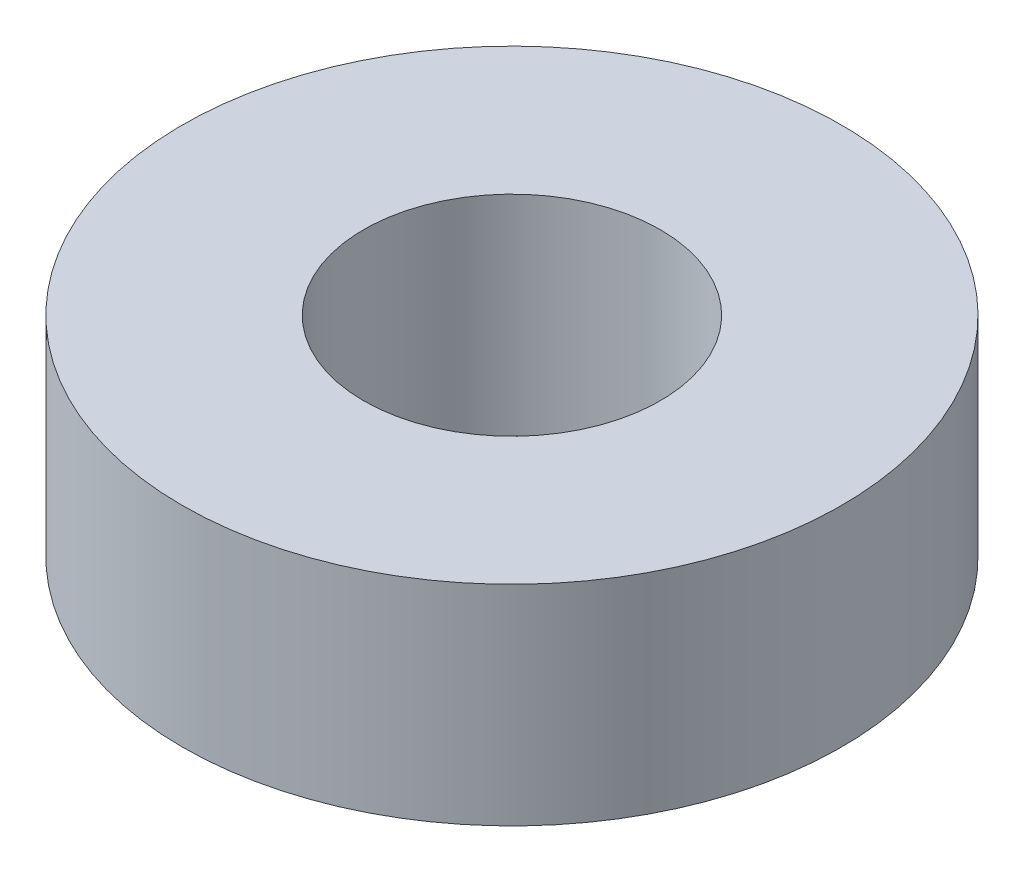
SolidWorks part; units mm, degrees
ref_plane "Front Plane" through (0, 0, 0) normal (0, 0, 1) x (1, 0, 0)
ref_plane "Top Plane" through (0, 0, 0) normal (0, 1, 0) x (1, 0, 0)
ref_plane "Right Plane" through (0, 0, 0) normal (1, 0, 0) x (0, 0, -1)
sketch "Sketch1" plane through (0, 0, 0) normal (0, 1, 0) x (1, 0, 0)
  circle A0 centre (0, 0) radius 2.25
  circle A1 centre (0, 0) radius 5
  dimension "D1" = 4.5
  dimension "D2" = 10
extrude "Boss-Extrude1" add sketch "Sketch1" along normal blind 3.175
